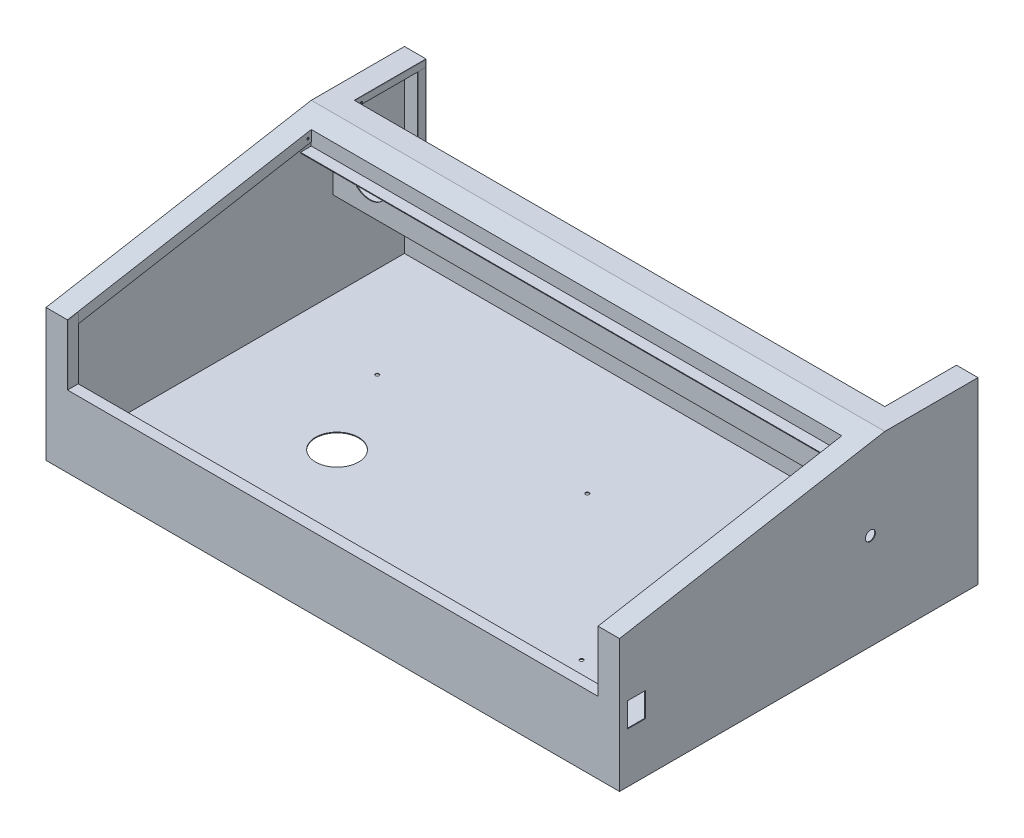
SolidWorks part; units mm, degrees
ref_plane "Alzado" through (0, 0, 0) normal (0, 0, 1) x (1, 0, 0)
ref_plane "Planta" through (0, 0, 0) normal (0, 1, 0) x (1, 0, 0)
ref_plane "Vista lateral" through (0, 0, 0) normal (1, 0, 0) x (0, 0, -1)
sketch "Croquis1" plane through (0, 0, 0) normal (0, 1, 0) x (1, 0, 0)
  line L1 (-400, -250) -> (400, -250)
  line L2 (-400, -250) -> (-400, 250)
  line L3 (-400, 250) -> (400, 250)
  line L4 (400, -250) -> (400, 250)
  line L5 (-400, -250) -> (400, 250) construction
  line L6 (-400, 250) -> (400, -250) construction
  point P0 (0, 0)
  dimension "D1" = 800
  dimension "D2" = 500
extrude "Saliente-Extruir1" add sketch "Croquis1" along normal blind 1
sketch "Croquis3" plane through (400, 0, 0) normal (1, 0, 0) x (0, 0, -1)
  line L0 (250, 1) -> (250, 0) construction
  line L1 (-250, 0) -> (250, 0)
  line L2 (-250, 0) -> (-250, 184.759)
  line L3 (250, 250) -> (120, 250)
  line L4 (250, 0) -> (250, 250)
  line L5 (-250, 0) -> (250, 0) construction
  line L6 (120, 250) -> (-250, 184.759)
  dimension "D1" = 80
  dimension "D2" = 250
  dimension "D3" = 130
extrude "Saliente-Extruir2" add sketch "Croquis3" against normal blind 1
sketch "Croquis4" plane through (-400, 0, 0) normal (-1, 0, 0) x (0, 0, 1)
  line L5 (-250, 250) -> (-250, 1)
  line L6 (-250, 1) -> (250, 1)
  line L7 (250, 1) -> (250, 184.759)
  line L8 (250, 184.759) -> (-120, 250)
  line L9 (-120, 250) -> (-250, 250)
  line L10 (-250, 250) -> (-250, 1)
  line L11 (-250, 1) -> (250, 1)
  line L12 (250, 1) -> (250, 184.759)
  line L13 (250, 184.759) -> (-120, 250)
  line L14 (-120, 250) -> (-250, 250)
  dimension "D1" = 0
extrude "Saliente-Extruir3" add sketch "Croquis4" against normal blind 1
sketch "Croquis5" plane through (0, 0, -250) normal (0, 0, -1) x (-1, 0, 0)
  line L1 (-400, 0) -> (400, 0)
  line L2 (-400, 0) -> (-400, 250)
  line L3 (-400, 250) -> (400, 250)
  line L4 (400, 0) -> (400, 250)
extrude "Saliente-Extruir4" add sketch "Croquis5" against normal blind 1
sketch "Croquis6" plane through (0, 0, 250) normal (0, 0, 1) x (1, 0, 0)
  line L1 (-400, 0) -> (400, 0)
  line L2 (-400, 0) -> (-400, 184.759)
  line L3 (-400, 184.759) -> (400, 184.759)
  line L4 (400, 0) -> (400, 184.759)
extrude "Saliente-Extruir5" add sketch "Croquis6" against normal blind 1
sketch "Croquis7" plane through (400, 0, 0) normal (1, 0, 0) x (0, 0, -1)
  line L0 (250, 250) -> (250, 249)
  line L1 (250, 249) -> (120, 249)
  line L2 (120, 249) -> (-250, 183.759)
  line L3 (-250, 183.759) -> (-250, 184.759)
  line L4 (-250, 184.759) -> (120, 250)
  line L5 (120, 250) -> (250, 250)
  line L6 (250, 250) -> (250, 0) construction
  dimension "D1" = 1
extrude "Saliente-Extruir8" add sketch "Croquis7" against normal blind 800
sketch "Croquis8" plane through (0, 250, -272.3986) normal (0, -1, 0) x (1, 0, 0)
  line L1 (-370, 182.3986) -> (370, 182.3986)
  line L2 (-370, 182.3986) -> (-370, 522.3986)
  line L3 (-370, 522.3986) -> (370, 522.3986)
  line L4 (370, 182.3986) -> (370, 522.3986)
  line L6 (-400, 522.3986) -> (-400, 152.3986) construction
  line L7 (400, 152.3986) -> (400, 522.3986) construction
  line L8 (-400, 152.3986) -> (400, 152.3986) construction
  line L10 (-400, 522.3986) -> (400, 522.3986) construction
  dimension "D1" = 30
  dimension "D2" = 30
  dimension "D3" = 30
extrude "Cortar-Extruir3" cut sketch "Croquis8" along normal blind 150
sketch "Croquis13" plane through (0, 100, 0) normal (0, 1, 0) x (1, 0, 0)
  line L0 (370, -250) -> (-370, -250) construction
  line L1 (-370, -250) -> (370, -250)
  line L2 (-370, -250) -> (-370, -235)
  line L3 (-370, -235) -> (370, -235)
  line L4 (370, -250) -> (370, -235)
  line L5 (370, -249) -> (370, -250) construction
  dimension "D1" = 15
extrude "Saliente-Extruir10" add sketch "Croquis13" against normal blind 1
sketch "Croquis14" plane through (370, 0, 0) normal (-1, 0, 0) x (0, 0, 1)
  line L1 (235, 100) -> (249, 100)
  line L2 (235, 100) -> (235, 186.4039)
  line L3 (235, 186.4039) -> (249, 183.9353)
  line L4 (249, 100) -> (249, 183.9353)
  line L10 (249, 100) -> (249, 183.9353) construction
  line L11 (249, 183.9353) -> (-90, 243.7102) construction
extrude "Saliente-Extruir21" add sketch "Croquis14" against normal blind 1 separate body
sketch "Croquis15" plane through (-370, 0, 0) normal (1, 0, 0) x (0, 0, -1)
  line L0 (-249, 100) -> (-235, 100)
  line L1 (-235, 100) -> (-235, 186.4039)
  line L2 (90, 243.7102) -> (-249, 183.9353) construction
  line L3 (-235, 186.4039) -> (-249, 183.9353)
  line L4 (-249, 183.9353) -> (-249, 100)
  line L5 (-249, 183.9353) -> (-249, 100) construction
extrude "Saliente-Extruir23" add sketch "Croquis15" against normal blind 1 separate body
sketch "Croquis16" plane through (370, 0, 0) normal (-1, 0, 0) x (0, 0, 1)
  line L0 (-90, 244.7102) -> (-92.6449, 229.7102)
  line L1 (-92.6449, 229.7102) -> (235, 171.9376)
  line L2 (235, 186.4039) -> (235, 100) construction
  line L3 (235, 171.9376) -> (235, 187.4039)
  line L4 (-90, 244.7102) -> (250, 184.759) construction
  line L5 (235, 187.4039) -> (-90, 244.7102)
  dimension "D1" = 15
extrude "Saliente-Extruir25" add sketch "Croquis16" against normal blind 1
sketch "Croquis18" plane through (0, 0, -90) normal (0, 0, 1) x (1, 0, 0)
  line L0 (370, 244.7102) -> (370, 224.7102)
  line L1 (370, 224.7102) -> (-370.1338, 224.7102)
  line L2 (-370.1338, 224.7102) -> (-370, 244.7102)
  line L3 (-370, 244.7102) -> (370, 244.7102) construction
  line L4 (-370, 244.7102) -> (370, 244.7102)
  dimension "D1" = 20
extrude "Saliente-Extruir31" add sketch "Croquis18" against normal blind 1
sketch "Croquis19" plane through (-370, 0, 0) normal (1, 0, 0) x (0, 0, -1)
  line L0 (90, 244.7102) -> (90, 229.7102)
  line L1 (90, 229.7102) -> (-235, 172.4039)
  line L3 (-235, 172.4039) -> (-235, 187.4039)
  line L4 (-250, 184.759) -> (90, 244.7102) construction
  line L5 (-235, 187.4039) -> (90, 244.7102)
  line L6 (-235, 100) -> (-235, 186.4039) construction
  dimension "D1" = 15
extrude "Saliente-Extruir32" add sketch "Croquis19" against normal blind 1
sketch "Croquis21" plane through (0, 224.7102, 0) normal (0, -1, 0) x (1, 0, 0)
  line L0 (370, -90) -> (370, 250) construction
  line L1 (-370, -90) -> (370, -90)
  line L2 (-370, -90) -> (-370, -75)
  line L3 (-370, -75) -> (370, -75)
  line L4 (370, -90) -> (370, -75)
  dimension "D1" = 15
extrude "Saliente-Extruir35" add sketch "Croquis21" along normal blind 1 separate body
sketch "Croquis22" plane through (0, 250, 0) normal (0, 1, 0) x (1, 0, 0)
  line L0 (-400, 250) -> (400, 250) construction
  line L1 (-370, 250) -> (370, 250)
  line L2 (-370, 250) -> (-370, 150)
  line L3 (-370, 150) -> (370, 150)
  line L4 (370, 250) -> (370, 150)
  line L5 (-370, -250) -> (-370, 90) construction
  line L6 (370, 90) -> (370, -250) construction
  line L7 (-400, 120) -> (400, 120) construction
  dimension "D1" = 30
extrude "Cortar-Extruir4" cut sketch "Croquis22" against normal blind 100
sketch "Croquis23" plane through (0, 0, -150) normal (0, 0, -1) x (-1, 0, 0)
  line L0 (-370, 249) -> (370, 249) construction
  line L1 (399, 249) -> (-399, 249)
  line L2 (399, 249) -> (399, 122)
  line L3 (399, 122) -> (-399, 122)
  line L4 (-399, 249) -> (-399, 122)
  dimension "D1" = 127
extrude "Saliente-Extruir36" add sketch "Croquis23" against normal blind 1
sketch "Croquis24" plane through (0, 0, -150) normal (0, 0, -1) x (-1, 0, 0)
  line L1 (-399, 122) -> (399, 122)
  line L2 (-399, 122) -> (-399, 121)
  line L3 (-399, 121) -> (399, 121)
  line L4 (399, 122) -> (399, 121)
  dimension "D1" = 1
extrude "Saliente-Extruir40" add sketch "Croquis24" along normal up to surface (99 mm away) separate body up to face at (0, 162.25, -249)
sketch "Croquis25" plane through (0, 0, -150) normal (0, 0, -1) x (-1, 0, 0)
  line L0 (370, 250) -> (-370, 250) construction
  line L1 (-370, 240) -> (370, 240)
  line L2 (-370, 240) -> (-370, 239)
  line L3 (-370, 239) -> (370, 239)
  line L4 (370, 240) -> (370, 239)
  line L5 (-370, 249) -> (-370, 250) construction
  line L6 (370, 249) -> (370, 250) construction
  dimension "D1" = 1
  dimension "D2" = 10
extrude "Saliente-Extruir41" add sketch "Croquis25" along normal blind 10
sketch "Croquis26" plane through (-370, 0, 0) normal (1, 0, 0) x (0, 0, -1)
  line L1 (150, 249) -> (249, 249)
  line L2 (150, 249) -> (150, 240)
  line L3 (150, 240) -> (249, 240)
  line L4 (249, 249) -> (249, 240)
  line L6 (249, 249) -> (249, 150) construction
  dimension "D1" = 9
extrude "Saliente-Extruir43" add sketch "Croquis26" against normal blind 1 separate body
sketch "Croquis27" plane through (370, 0, 0) normal (-1, 0, 0) x (0, 0, 1)
  line L0 (-249, 150) -> (-249, 249) construction
  line L1 (-150, 249) -> (-249, 249)
  line L2 (-150, 249) -> (-150, 240)
  line L3 (-150, 240) -> (-249, 240)
  line L4 (-249, 249) -> (-249, 240)
  line L5 (-160, 240) -> (-150, 240) construction
extrude "Saliente-Extruir45" add sketch "Croquis27" against normal blind 1 separate body
sketch "Croquis28" plane through (-370, 0, 0) normal (1, 0, 0) x (0, 0, -1)
  line L0 (250, 150) -> (249, 150) construction
  line L1 (249, 240) -> (239, 240)
  line L2 (249, 240) -> (249, 150)
  line L3 (249, 150) -> (239, 150)
  line L4 (239, 240) -> (239, 150)
  dimension "D1" = 10
extrude "Saliente-Extruir47" add sketch "Croquis28" against normal blind 1 separate body
sketch "Croquis29" plane through (0, 150, 0) normal (0, 1, 0) x (1, 0, 0)
  line L0 (370, 249) -> (370, 250) construction
  line L1 (-370, 249) -> (370, 249)
  line L2 (-370, 249) -> (-370, 239)
  line L3 (-370, 239) -> (370, 239)
  line L4 (370, 249) -> (370, 239)
  line L5 (-370, 239) -> (-370, 249) construction
extrude "Saliente-Extruir48" add sketch "Croquis29" against normal blind 1 separate body
sketch "Croquis30" plane through (370, 0, 0) normal (-1, 0, 0) x (0, 0, 1)
  line L1 (-249, 240) -> (-239, 240)
  line L2 (-249, 240) -> (-249, 150)
  line L3 (-249, 150) -> (-239, 150)
  line L4 (-239, 240) -> (-239, 150)
extrude "Saliente-Extruir49" add sketch "Croquis30" against normal blind 1 separate body
sketch "Croquis31" plane through (0, 0, -250) normal (0, 0, -1) x (-1, 0, 0)
  line L0 (-400, 0) -> (400, 0) construction
  line L1 (50, 95) -> (230, 95)
  line L2 (50, 95) -> (50, 45)
  line L3 (50, 45) -> (230, 45)
  line L4 (230, 95) -> (230, 45)
  line L5 (-350, 52) -> (-338, 52)
  line L6 (-360, 42) -> (-360, 20)
  line L7 (-360, 20) -> (-328, 20)
  line L8 (-328, 42) -> (-328, 20)
  line L9 (-310, 70) -> (-275, 70)
  line L10 (-310, 70) -> (-310, 33)
  line L11 (-310, 33) -> (-275, 33)
  line L12 (-275, 70) -> (-275, 33)
  line L13 (-251, 70) -> (-216, 70)
  line L14 (-251, 70) -> (-251, 33)
  line L15 (-251, 33) -> (-216, 33)
  line L16 (-216, 70) -> (-216, 33)
  line L17 (400, 250) -> (400, 0) construction
  line L18 (-360, 42) -> (-350, 52)
  line L19 (-338, 52) -> (-328, 42)
  line L20 (-400, 250) -> (-400, 0) construction
  circle A0 centre (-79, 91) radius 6
  circle A1 centre (-90, 30) radius 6
  circle A2 centre (-30, 30) radius 6
  circle A3 centre (300, 85) radius 6
  point P4 (-360, 52)
  point P7 (-328, 52)
  dimension "D16" = 12
  dimension "D1" = 180
  dimension "D2" = 50
  dimension "D3" = 45
  dimension "D4" = 170
  dimension "D5" = 37
  dimension "D6" = 35
  dimension "D7" = 32
  dimension "D8" = 32
  dimension "D9" = 20
  dimension "D10" = 40
  dimension "D13" = 33
  dimension "D14" = 90
  dimension "D15" = 24
  dimension "D17" = 60
  dimension "D18" = 30
  dimension "D19" = 310
  dimension "D20" = 321
  dimension "D21" = 91
  dimension "D22" = 100
  dimension "D23" = 85
extrude "Cortar-Extruir5" cut sketch "Croquis31" against normal up to next (1 mm away)
sketch "Croquis35" plane through (400, 0, 0) normal (1, 0, 0) x (0, 0, -1)
  line L0 (-250, 0) -> (250, 0) construction
  line L1 (-239, 104) -> (-214, 104)
  line L2 (-239, 104) -> (-239, 70)
  line L3 (-239, 70) -> (-214, 70)
  line L4 (-214, 104) -> (-214, 70)
  line L5 (-250, 184.759) -> (-250, 0) construction
  dimension "D1" = 25
  dimension "D2" = 34
  dimension "D3" = 70
  dimension "D4" = 11
sketch "Croquis36" plane through (400, 0, 0) normal (1, 0, 0) x (0, 0, -1)
  line L0 (-250, 0) -> (250, 0) construction
  line L1 (250, 250) -> (250, 0) construction
  circle A0 centre (100, 134) radius 7
  dimension "D1" = 14
  dimension "D3" = 150
  dimension "D2" = 134
extrude "Cortar-Extruir8" cut sketch "Croquis35" against normal up to next (1 mm away)
extrude "Cortar-Extruir9" cut sketch "Croquis36" against normal up to next (1 mm away)
sketch "Croquis37" plane through (0, 1, 0) normal (0, 1, 0) x (1, 0, 0)
  line L0 (-400, -250) -> (400, -250) construction
  line L1 (400, -250) -> (400, 250) construction
  line L2 (-400, 250) -> (-400, -250) construction
  line L3 (400, 250) -> (-400, 250) construction
  circle A0 centre (-209, -35) radius 30
  circle A1 centre (261, 3) radius 30
  circle A2 centre (325.5, -118.5) radius 2.5
  circle A3 centre (325.5, 39.5) radius 2.5
  circle A4 centre (215.5, 39.5) radius 2.5
  circle A5 centre (215.5, -118.5) radius 2.5
  circle A6 centre (18.5, -164.5) radius 2.5
  circle A7 centre (-106.5, -164.5) radius 2.5
  circle A8 centre (-271.5, -164.5) radius 2.5
  circle A9 centre (18.5, 86.5) radius 2.5
  circle A10 centre (-271.5, 83.5) radius 2.5
  circle A11 centre (195, -214) radius 8.5
  circle A12 centre (320, -214) radius 8.5
  dimension "D1" = 60
  dimension "D2" = 60
  dimension "D3" = 5
  dimension "D4" = 253
  dimension "D5" = 139
  dimension "D7" = 131.5
  dimension "D10" = 191
  dimension "D11" = 215
  dimension "D20" = 17
  dimension "D22" = 80
  dimension "D23" = 36
  dimension "D13" = 165
  dimension "D6" = 74.5
  dimension "D8" = 158
  dimension "D9" = 110
  dimension "D12" = 128.5
  dimension "D15" = 85.5
  dimension "D17" = 166.5
  dimension "D18" = 290
  dimension "D19" = 163.5
  dimension "D21" = 125
extrude "Cortar-Extruir11" cut sketch "Croquis37" against normal up to next (1 mm away)
ref_plane "Plano1" through (124, 0, 0) normal (-1, 0, 0) x (0, 0, 1)
sketch "Croquis40" plane through (-370, 0, 0) normal (1, 0, 0) x (0, 0, -1)
  line L0 (86.6612, 229.1215) -> (84.096, 243.6692) construction
  line L1 (-235, 172.4039) -> (90, 229.7102) construction
  line L2 (-250, 184.759) -> (90, 244.7102) construction
  line L3 (90, 229.7102) -> (90, 244.7102) construction
  circle A0 centre (85.4852, 235.7907) radius 1.5
  dimension "D1" = 3
  dimension "D2" = 10
  dimension "D3" = 8
extrude "Cortar-Extruir12" cut sketch "Croquis40" against normal blind 1
sketch "Croquis41" plane through (-370, 0, 0) normal (1, 0, 0) x (0, 0, -1)
  circle A0 centre (160, 242) radius 1.5
  dimension "D1" = 3
extrude "Cortar-Extruir13" cut sketch "Croquis41" against normal blind 1
sketch "Croquis42" plane through (0, 0, -149) normal (0, 0, 1) x (1, 0, 0)
  line L0 (-399, 122) -> (-399, 249) construction
  line L1 (399, 122) -> (-399, 122) construction
  circle A0 centre (-347.85, 165.95) radius 24.75
  dimension "D1" = 49.5
  dimension "D2" = 51.15
  dimension "D3" = 43.95
extrude "Cortar-Extruir14" cut sketch "Croquis42" against normal up to next (1 mm away)
